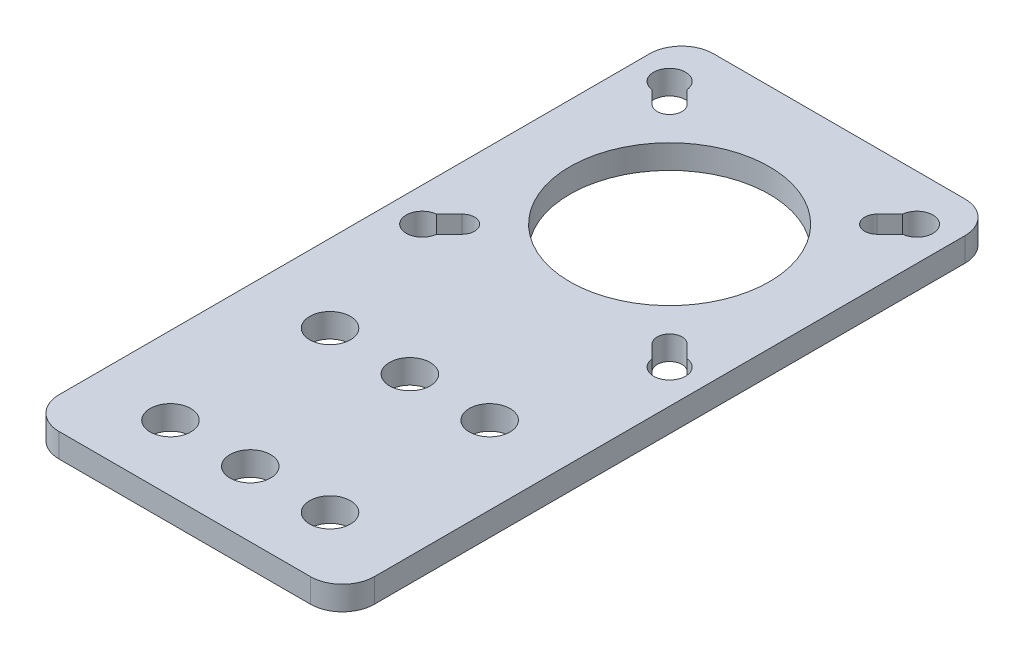
SolidWorks part; units mm, degrees
material "6061-T6 (SS)"
ref_plane "Front Plane" through (0, 0, 0) normal (0, 0, 1) x (1, 0, 0)
ref_plane "Top Plane" through (0, 0, 0) normal (0, 1, 0) x (1, 0, 0)
ref_plane "Right Plane" through (0, 0, 0) normal (1, 0, 0) x (0, 0, -1)
sketch "Sketch1" plane through (0, 0, 0) normal (0, 1, 0) x (1, 0, 0)
  line L0 (0, 0) -> (30, 0) construction
  line L1 (15.75, -60.75) -> (-15.75, -60.75)
  line L2 (19.75, -56.75) -> (19.75, 17.25)
  line L3 (15.75, 21.25) -> (-15.75, 21.25)
  line L4 (-19.75, -56.75) -> (-19.75, 17.25)
  line L5 (0, 21.25) -> (0, 0) construction
  line L6 (13, 13) -> (15.5, 15.5) construction
  line L7 (11.904, 14.096) -> (14.404, 16.596)
  line L8 (14.096, 11.904) -> (16.596, 14.404)
  line L9 (10, -52.55) -> (0, -52.55) construction
  line L10 (-13, 13) -> (-15.5, 15.5) construction
  line L11 (-11.904, 14.096) -> (-14.404, 16.596)
  line L12 (-14.096, 11.904) -> (-16.596, 14.404)
  line L13 (-13, -13) -> (-15.5, -15.5) construction
  line L14 (-11.904, -14.096) -> (-14.404, -16.596)
  line L15 (-14.096, -11.904) -> (-16.596, -14.404)
  line L16 (13, -13) -> (15.5, -15.5) construction
  line L17 (11.904, -14.096) -> (14.404, -16.596)
  line L18 (14.096, -11.904) -> (16.596, -14.404)
  line L22 (0, 0) -> (27.1737, 27.1737) construction
  arc A0 (-15.75, -60.75) -> (-19.75, -56.75) centre (-15.75, -56.75) cw
  arc A1 (15.75, -60.75) -> (19.75, -56.75) centre (15.75, -56.75) ccw
  arc A2 (19.75, 17.25) -> (15.75, 21.25) centre (15.75, 17.25) ccw
  arc A3 (-15.75, 21.25) -> (-19.75, 17.25) centre (-15.75, 17.25) ccw
  circle A4 centre (0, 0) radius 12.5
  arc A5 (11.904, 14.096) -> (14.096, 11.904) centre (13, 13) ccw
  arc A6 (16.596, 14.404) -> (14.404, 16.596) centre (15.5, 15.5) ccw
  circle A7 centre (10, -52.55) radius 2.55
  circle A8 centre (10, -32.55) radius 2.55
  circle A9 centre (0, -52.55) radius 2.55
  circle A10 centre (0, -32.55) radius 2.55
  circle A11 centre (-10, -52.55) radius 2.55
  circle A12 centre (-10, -32.55) radius 2.55
  arc A13 (-11.904, 14.096) -> (-14.096, 11.904) centre (-13, 13) cw
  arc A14 (-16.596, 14.404) -> (-14.404, 16.596) centre (-15.5, 15.5) cw
  arc A15 (-11.904, -14.096) -> (-14.096, -11.904) centre (-13, -13) ccw
  arc A16 (-16.596, -14.404) -> (-14.404, -16.596) centre (-15.5, -15.5) ccw
  arc A17 (11.904, -14.096) -> (14.096, -11.904) centre (13, -13) cw
  arc A18 (16.596, -14.404) -> (14.404, -16.596) centre (15.5, -15.5) cw
  point P4 (14.25, 14.25)
  point P40 (-14.25, 14.25)
  point P47 (-14.25, -14.25)
  point P54 (14.25, -14.25)
  dimension "D2" = 4
  dimension "D3" = 60.75
  dimension "D5" = 3.1
  dimension "D7" = 20
  dimension "D10" = 3
  dimension "D4" = 25
  dimension "D8" = 9.75
  dimension "D14" = 8.25
  dimension "D6" = 5.1
  dimension "D1" = 82
  dimension "D9" = 39.5
  dimension "D11" = 10
  dimension "D12" = 8.2
  dimension "D13" = 5.75
  dimension "D16" = 45
extrude "Boss-Extrude1" add sketch "Sketch1" along normal blind 3
sketch "Sketch2" plane through (0, 3, 0) normal (0, 1, 0) x (1, 0, 0)
  circle A0 centre (-15.5, 15.5) radius 2
  circle A1 centre (15.5, 15.5) radius 2
  circle A2 centre (-15.5, -15.5) radius 2
  circle A3 centre (15.5, -15.5) radius 2
extrude "Cut-Extrude1" cut sketch "Sketch2" against normal blind 10
